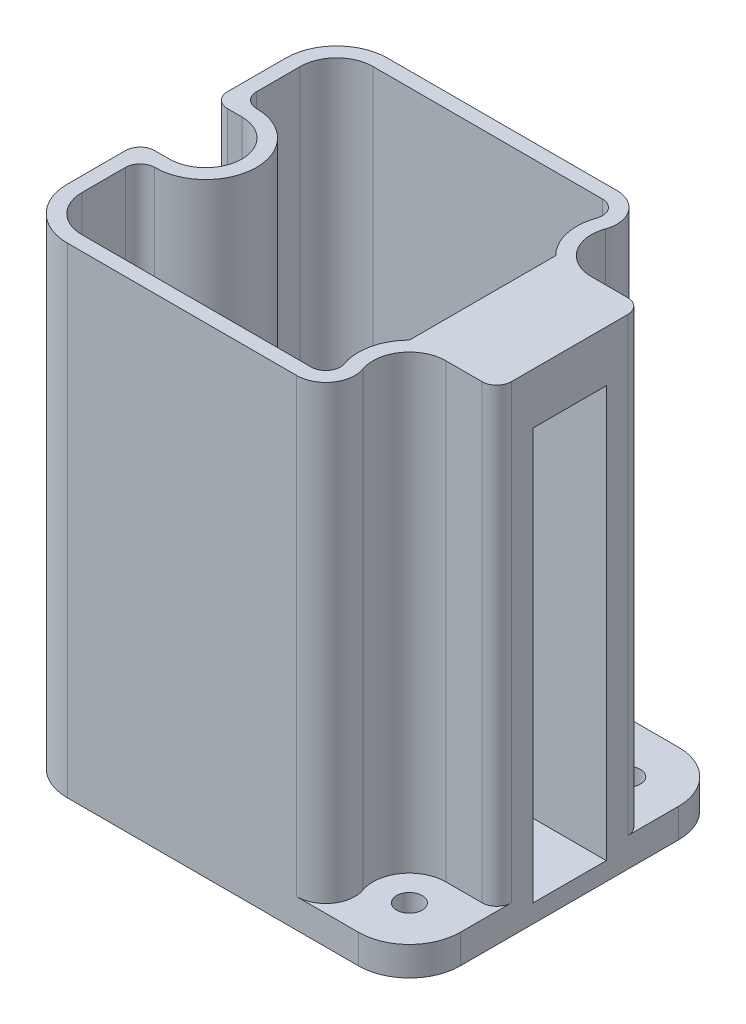
SolidWorks part; units mm, degrees
ref_plane "Alzado" through (0, 0, 0) normal (0, 0, 1) x (1, 0, 0)
ref_plane "Planta" through (0, 0, 0) normal (0, 1, 0) x (1, 0, 0)
ref_plane "Vista lateral" through (0, 0, 0) normal (1, 0, 0) x (0, 0, -1)
sketch "Croquis1" plane through (0, 89.4998, 0) normal (0, 1, 0) x (1, 0, 0)
  line L0 (-45.1183, 8.085) -> (-13.6035, 8.085)
  line L1 (-0.1183, 21.5703) -> (-0.1183, 34.5997) construction
  line L2 (-13.6035, 48.085) -> (-45.1183, 48.085)
  line L3 (-50.1183, 43.085) -> (-50.1183, 37.085)
  line L4 (-45.1183, 6.085) -> (-5.1183, 6.085)
  line L5 (1.8817, 13.085) -> (1.8817, 43.085)
  line L6 (-5.1183, 50.085) -> (-45.1183, 50.085)
  line L7 (-52.1183, 43.085) -> (-52.1183, 13.085)
  line L8 (-45.1183, 6.085) -> (-5.1183, 6.085)
  line L9 (1.8817, 13.085) -> (1.8817, 43.085)
  line L10 (-5.1183, 50.085) -> (-45.1183, 50.085)
  line L11 (-52.1183, 43.085) -> (-52.1183, 13.085)
  line L12 (-50.1183, 19.085) -> (-50.1183, 13.085)
  line L13 (-0.1183, 13.085) -> (-0.1183, 43.085) construction
  line L14 (-45.1183, 8.085) -> (-5.1183, 8.085) construction
  line L15 (-5.1183, 48.085) -> (-45.1183, 48.085) construction
  line L17 (-50.1183, 43.085) -> (-50.1183, 13.085) construction
  line L25 (-10.068, 38.1352) -> (-10.068, 18.0347)
  arc A2 (-45.1183, 48.085) -> (-50.1183, 43.085) centre (-45.1183, 43.085) ccw
  arc A3 (-50.1183, 13.085) -> (-45.1183, 8.085) centre (-45.1183, 13.085) ccw
  arc A4 (-52.1183, 13.085) -> (-45.1183, 6.085) centre (-45.1183, 13.085) ccw
  arc A5 (-5.1183, 6.085) -> (1.8817, 13.085) centre (-5.1183, 13.085) ccw
  arc A6 (1.8817, 43.085) -> (-5.1183, 50.085) centre (-5.1183, 43.085) ccw
  arc A7 (-45.1183, 50.085) -> (-52.1183, 43.085) centre (-45.1183, 43.085) ccw
  arc A8 (-52.1183, 13.085) -> (-45.1183, 6.085) centre (-45.1183, 13.085) ccw
  arc A11 (-45.1183, 50.085) -> (-52.1183, 43.085) centre (-45.1183, 43.085) ccw
  arc A12 (-5.1183, 6.085) -> (1.8817, 13.085) centre (-5.1183, 13.085) ccw
  arc A13 (1.8817, 43.085) -> (-5.1183, 50.085) centre (-5.1183, 43.085) ccw
  arc A14 (-48.1183, 21.085) -> (-48.1183, 35.085) centre (-48.1183, 28.085) ccw
  arc A15 (-5.1183, 6.085) -> (1.8817, 13.085) centre (-5.1183, 13.085) ccw construction
  arc A16 (-2.7849, 19.6846) -> (-11.7179, 10.7516) centre (-5.1183, 13.085) ccw construction
  arc A17 (-5.1183, 8.085) -> (-0.1183, 13.085) centre (-5.1183, 13.085) ccw construction
  arc A18 (1.8817, 43.085) -> (-5.1183, 50.085) centre (-5.1183, 43.085) ccw construction
  arc A19 (-11.7179, 45.4183) -> (-2.7849, 36.4853) centre (-5.1183, 43.085) ccw construction
  arc A20 (-0.1183, 43.085) -> (-5.1183, 48.085) centre (-5.1183, 43.085) ccw construction
  arc A21 (-11.7179, 45.4183) -> (-13.6035, 48.085) centre (-13.6035, 46.085) ccw
  arc A22 (-0.1183, 34.5997) -> (-2.7849, 36.4853) centre (-2.1183, 34.5997) ccw construction
  arc A23 (-13.6035, 8.085) -> (-11.7179, 10.7516) centre (-13.6035, 10.085) ccw
  arc A24 (-2.7849, 19.6846) -> (-0.1183, 21.5703) centre (-2.1183, 21.5703) ccw construction
  arc A25 (-48.1183, 21.085) -> (-50.1183, 19.085) centre (-48.1183, 19.085) ccw
  arc A26 (-48.1183, 35.085) -> (-50.1183, 37.085) centre (-48.1183, 37.085) cw
  circle A27 centre (-48.1183, 28.085) radius 1.75 construction
  circle A28 centre (-5.1183, 43.085) radius 1.75 construction
  circle A29 centre (-5.1183, 13.085) radius 1.75 construction
  circle A30 centre (-48.1183, 28.085) radius 1.75
  circle A31 centre (-5.1183, 43.085) radius 1.75
  circle A32 centre (-5.1183, 13.085) radius 1.75
  arc A33 (-11.7179, 45.4183) -> (-10.068, 38.1352) centre (-5.1183, 43.085) ccw
  arc A34 (-11.7179, 10.7516) -> (-10.068, 18.0347) centre (-5.1183, 13.085) cw
  point P42 (-50.1183, 21.3768)
  dimension "D3" = 2
  dimension "D1" = 0
  dimension "D2" = 2
extrude "Saliente-Extruir1" add sketch "Croquis1" along normal blind 2
sketch "Croquis2" plane through (0, 91.4998, 0) normal (0, 1, 0) x (1, 0, 0)
  line L0 (-10.068, 18.0347) -> (-10.068, 38.1352) construction
  line L1 (-45.1183, 8.085) -> (-13.6035, 8.085) construction
  line L2 (-50.1183, 19.085) -> (-50.1183, 13.085) construction
  line L3 (-50.1183, 43.085) -> (-50.1183, 37.085) construction
  line L4 (-45.1183, 6.085) -> (-5.1183, 6.085)
  line L5 (1.8817, 13.085) -> (1.8817, 43.085)
  line L6 (-5.1183, 50.085) -> (-45.1183, 50.085)
  line L7 (-52.1183, 43.085) -> (-52.1183, 13.085)
  line L8 (-45.1183, 6.085) -> (-5.1183, 6.085)
  line L9 (1.8817, 13.085) -> (1.8817, 43.085)
  line L10 (-5.1183, 50.085) -> (-45.1183, 50.085)
  line L11 (-52.1183, 43.085) -> (-52.1183, 13.085)
  line L12 (-13.6035, 48.085) -> (-45.1183, 48.085) construction
  line L13 (-10.068, 18.0347) -> (-10.068, 38.1352)
  line L14 (-45.1183, 8.085) -> (-13.6035, 8.085)
  line L15 (-50.1183, 19.085) -> (-50.1183, 13.085)
  line L16 (-50.1183, 43.085) -> (-50.1183, 37.085)
  line L17 (-13.6035, 48.085) -> (-45.1183, 48.085)
  arc A0 (-10.068, 18.0347) -> (-11.7179, 10.7516) centre (-5.1183, 13.085) ccw construction
  arc A1 (-13.6035, 8.085) -> (-11.7179, 10.7516) centre (-13.6035, 10.085) ccw construction
  arc A2 (-50.1183, 13.085) -> (-45.1183, 8.085) centre (-45.1183, 13.085) ccw construction
  arc A3 (-48.1183, 21.085) -> (-50.1183, 19.085) centre (-48.1183, 19.085) ccw construction
  arc A4 (-52.1183, 13.085) -> (-45.1183, 6.085) centre (-45.1183, 13.085) ccw
  arc A5 (-5.1183, 6.085) -> (1.8817, 13.085) centre (-5.1183, 13.085) ccw
  arc A6 (1.8817, 43.085) -> (-5.1183, 50.085) centre (-5.1183, 43.085) ccw
  arc A7 (-45.1183, 50.085) -> (-52.1183, 43.085) centre (-45.1183, 43.085) ccw
  arc A8 (-52.1183, 13.085) -> (-45.1183, 6.085) centre (-45.1183, 13.085) ccw
  arc A9 (-5.1183, 6.085) -> (1.8817, 13.085) centre (-5.1183, 13.085) ccw
  arc A10 (1.8817, 43.085) -> (-5.1183, 50.085) centre (-5.1183, 43.085) ccw
  arc A11 (-45.1183, 50.085) -> (-52.1183, 43.085) centre (-45.1183, 43.085) ccw
  arc A12 (-48.1183, 21.085) -> (-48.1183, 35.085) centre (-48.1183, 28.085) ccw construction
  arc A13 (-50.1183, 37.085) -> (-48.1183, 35.085) centre (-48.1183, 37.085) ccw construction
  arc A14 (-45.1183, 48.085) -> (-50.1183, 43.085) centre (-45.1183, 43.085) ccw construction
  arc A15 (-11.7179, 45.4183) -> (-13.6035, 48.085) centre (-13.6035, 46.085) ccw construction
  arc A16 (-11.7179, 45.4183) -> (-10.068, 38.1352) centre (-5.1183, 43.085) ccw construction
  arc A17 (-10.068, 18.0347) -> (-11.7179, 10.7516) centre (-5.1183, 13.085) ccw
  arc A18 (-13.6035, 8.085) -> (-11.7179, 10.7516) centre (-13.6035, 10.085) ccw
  arc A19 (-50.1183, 13.085) -> (-45.1183, 8.085) centre (-45.1183, 13.085) ccw
  arc A20 (-48.1183, 21.085) -> (-50.1183, 19.085) centre (-48.1183, 19.085) ccw
  arc A21 (-48.1183, 21.085) -> (-48.1183, 35.085) centre (-48.1183, 28.085) ccw
  arc A22 (-50.1183, 37.085) -> (-48.1183, 35.085) centre (-48.1183, 37.085) ccw
  arc A23 (-45.1183, 48.085) -> (-50.1183, 43.085) centre (-45.1183, 43.085) ccw
  arc A24 (-11.7179, 45.4183) -> (-13.6035, 48.085) centre (-13.6035, 46.085) ccw
  arc A25 (-11.7179, 45.4183) -> (-10.068, 38.1352) centre (-5.1183, 43.085) ccw
  circle A26 centre (-48.1183, 28.085) radius 1.75 construction
  circle A27 centre (-5.1183, 43.085) radius 1.75 construction
  circle A28 centre (-5.1183, 13.085) radius 1.75 construction
  circle A29 centre (-48.1183, 28.085) radius 1.75
  circle A30 centre (-5.1183, 43.085) radius 1.75
  circle A31 centre (-5.1183, 13.085) radius 1.75
  dimension "D1" = 0
extrude "Saliente-Extruir2" add sketch "Croquis2" along normal blind 64
sketch "Croquis3" plane through (0, 155.4998, 0) normal (0, 1, 0) x (1, 0, 0)
  line L0 (-5.1183, 38.085) -> (1.8817, 38.085)
  line L1 (1.8817, 13.085) -> (1.8817, 43.085) construction
  line L2 (-5.1183, 18.085) -> (1.8817, 18.085)
  line L3 (-5.1183, 50.085) -> (-45.1183, 50.085) construction
  line L4 (-45.1183, 6.085) -> (-5.1183, 6.085) construction
  line L5 (-5.1183, 50.085) -> (-13.6035, 50.085)
  line L6 (1.8817, 13.085) -> (1.8817, 18.085)
  line L7 (-13.6035, 6.085) -> (-5.1183, 6.085)
  line L8 (1.8817, 38.085) -> (1.8817, 43.085)
  line L9 (-48.1183, 23.085) -> (-52.1183, 23.085)
  line L10 (-52.1183, 43.085) -> (-52.1183, 13.085) construction
  line L12 (-48.1183, 33.085) -> (-52.1183, 33.085)
  line L13 (-52.1183, 33.085) -> (-52.1183, 23.085)
  arc A10 (-8.6538, 16.6205) -> (-9.8323, 11.4183) centre (-5.1183, 13.085) ccw
  arc A11 (-13.6035, 6.085) -> (-9.8323, 11.4183) centre (-13.6035, 10.085) ccw
  arc A12 (-8.6538, 16.6205) -> (-9.8323, 11.4183) centre (-5.1183, 13.085) ccw
  arc A13 (-13.6035, 6.085) -> (-9.8323, 11.4183) centre (-13.6035, 10.085) ccw
  arc A15 (-8.6538, 16.6205) -> (-5.1183, 18.085) centre (-5.1183, 13.085) cw
  arc A16 (-8.6538, 39.5494) -> (-5.1183, 38.085) centre (-5.1183, 43.085) ccw
  arc A17 (-9.8323, 44.7516) -> (-8.6538, 39.5494) centre (-5.1183, 43.085) ccw
  arc A18 (-9.8323, 44.7516) -> (-13.6035, 50.085) centre (-13.6035, 46.085) ccw
  arc A19 (-9.8323, 44.7516) -> (-8.6538, 39.5494) centre (-5.1183, 43.085) ccw
  arc A20 (-9.8323, 44.7516) -> (-13.6035, 50.085) centre (-13.6035, 46.085) ccw
  arc A21 (1.8817, 43.085) -> (-5.1183, 50.085) centre (-5.1183, 43.085) ccw construction
  arc A22 (-5.1183, 6.085) -> (1.8817, 13.085) centre (-5.1183, 13.085) ccw construction
  arc A23 (1.8817, 43.085) -> (-5.1183, 50.085) centre (-5.1183, 43.085) ccw
  arc A24 (-5.1183, 6.085) -> (1.8817, 13.085) centre (-5.1183, 13.085) ccw
  arc A27 (-48.1183, 23.085) -> (-48.1183, 33.085) centre (-48.1183, 28.085) ccw
  arc A28 (-48.1183, 23.085) -> (-48.1183, 33.085) centre (-48.1183, 28.085) ccw
  dimension "D3" = 2
  dimension "D1" = 2
  dimension "D2" = 2
extrude "Cortar-Extruir1" cut sketch "Croquis3" against normal blind 62
fillet "Redondeo1" radius 2 4 edges at (1.8817, 124.4998, -38.085) (1.8817, 124.4998, -18.085) (-52.1183, 124.4998, -23.085) (-52.1183, 124.4998, -33.085)
sketch "Croquis5" plane through (1.8817, 0, 0) normal (1, 0, 0) x (0, 0, -1)
  line L0 (20.085, 155.4998) -> (36.085, 155.4998) construction
  line L1 (23.035, 91.9998) -> (33.135, 91.9998)
  line L2 (23.035, 91.9998) -> (23.035, 148.4998)
  line L3 (23.035, 148.4998) -> (33.135, 148.4998)
  line L4 (33.135, 91.9998) -> (33.135, 148.4998)
  line L5 (23.035, 91.9998) -> (33.135, 148.4998) construction
  line L6 (23.035, 148.4998) -> (33.135, 91.9998) construction
  point P0 (28.085, 120.2498)
  point P7 (28.085, 155.4998)
  point P8 (0, 0)
  dimension "D1" = 7
  dimension "D2" = 56.5
  dimension "D3" = 10.1
extrude "Cortar-Extruir2" cut sketch "Croquis5" against normal up to next
